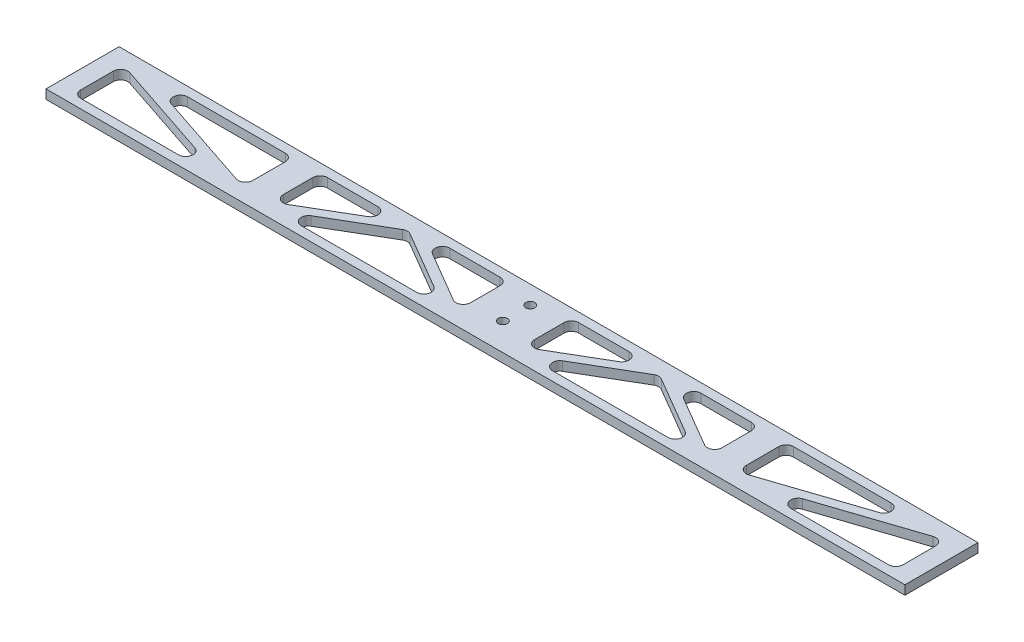
SolidWorks part; units mm, degrees
material "Plywood"
ref_plane "Front Plane" through (0, 0, 0) normal (0, 0, 1) x (1, 0, 0)
ref_plane "Top Plane" through (0, 0, 0) normal (0, 1, 0) x (1, 0, 0)
ref_plane "Right Plane" through (0, 0, 0) normal (1, 0, 0) x (0, 0, -1)
sketch "Sketch1" plane through (0, 0, 0) normal (0, 1, 0) x (1, 0, 0)
  line L1 (149.225, -12.7) -> (-149.225, -12.7)
  line L2 (149.225, -12.7) -> (149.225, 12.7)
  line L3 (149.225, 12.7) -> (-149.225, 12.7)
  line L4 (-149.225, -12.7) -> (-149.225, 12.7)
  point P0 (0, 12.7)
  point P6 (-149.225, 0)
  dimension "D1" = 25.4
  dimension "D2" = 298.45
extrude "Boss-Extrude1" add sketch "Sketch1" along normal blind 3.175
sketch "Sketch2" plane through (0, 3.175, 0) normal (0, 1, 0) x (1, 0, 0)
  line L0 (149.225, -12.7) -> (149.225, 12.7) construction
  line L2 (-149.225, 12.7) -> (-149.225, -12.7) construction
  line L4 (149.225, -12.7) -> (149.225, 12.7)
  line L6 (-149.225, 12.7) -> (-149.225, -12.7)
  line L8 (149.225, 9.525) -> (-149.225, 9.525)
  line L9 (-149.225, -9.525) -> (149.225, -9.525)
  line L10 (-142.875, 9.525) -> (-142.875, -9.525)
  line L11 (-80.9625, 9.525) -> (-80.9625, -9.525) construction
  line L12 (142.875, 9.525) -> (142.875, -9.525)
  line L13 (0, -9.525) -> (0, 9.525) construction
  line L14 (11.1125, 9.525) -> (11.1125, -9.525)
  line L15 (-11.1125, 9.525) -> (-11.1125, -9.525)
  line L16 (-85.725, 9.525) -> (-85.725, -9.525)
  line L17 (-76.2, 9.525) -> (-76.2, -9.525)
  line L18 (80.9625, 9.525) -> (80.9625, -9.525) construction
  line L19 (85.725, 9.525) -> (85.725, -9.525)
  line L20 (76.2, 9.525) -> (76.2, -9.525)
  line L21 (-76.2, -9.525) -> (-43.6562, 9.525)
  line L22 (-43.6562, 9.525) -> (-11.1125, -9.525)
  line L23 (-85.725, -9.525) -> (-142.875, 9.525)
  line L24 (11.1125, -9.525) -> (43.6562, 9.525)
  line L25 (43.6562, 9.525) -> (76.2, -9.525)
  line L26 (85.725, -9.525) -> (142.875, 9.525)
  line L27 (-85.223, -8.019) -> (-142.373, 11.031)
  line L28 (-75.398, -10.895) -> (-43.6562, 7.6855)
  line L29 (-43.6562, 7.6855) -> (-11.9145, -10.895)
  line L30 (11.9145, -10.895) -> (43.6562, 7.6855)
  line L31 (43.6562, 7.6855) -> (75.398, -10.895)
  line L32 (86.227, -11.031) -> (143.377, 8.019)
  line L33 (-86.227, -11.031) -> (-143.377, 8.019)
  line L34 (-77.002, -8.155) -> (-43.6562, 11.3645)
  line L35 (-43.6562, 11.3645) -> (-10.3105, -8.155)
  line L36 (10.3105, -8.155) -> (43.6562, 11.3645)
  line L37 (43.6562, 11.3645) -> (77.002, -8.155)
  line L38 (85.223, -8.019) -> (142.373, 11.031)
  dimension "D1" = 3.175
  dimension "D2" = 3.175
  dimension "D3" = 6.35
  dimension "D4" = 6.35
  dimension "D11" = 4.7625
  dimension "D12" = 4.7625
  dimension "D8" = 9.525
  dimension "D9" = 4.7625
  dimension "D7" = 63.5
  dimension "D10" = 63.5
  dimension "D5" = 22.225
  dimension "D6" = 11.1125
  dimension "D13" = 1.5875
  dimension "D14" = 1.5875
extrude "Cut-Extrude1" cut sketch "Sketch2" against normal through all contours L9 L33 L10 | L27 L16 L8 | L17 L34 L8 | L29 L28 L9 | L8 L35 L15 | L14 L36 L8 | L31 L30 L9 | L8 L37 L20 | L19 L38 L8 | L32 L9 L12
sketch "Sketch3" plane through (0, 3.175, 0) normal (0, 1, 0) x (1, 0, 0)
  circle A0 centre (0, 6.35) radius 1.5875
  circle A1 centre (0, -3.175) radius 1.5875
  dimension "D1" = 3.175
  dimension "D2" = 9.525
  dimension "D3" = 6.35
extrude "Cut-Extrude2" cut sketch "Sketch3" against normal through all
fillet "Fillet1" radius 2.54 30 edges at (-14.2549, 1.5875, 9.525) (-73.0576, 1.5875, 9.525) (-43.6562, 1.5875, -7.6855) (-11.1125, 1.5875, 7.6855) (-40.5138, 1.5875, -9.525) (-11.1125, 1.5875, -9.525) (-46.7987, 1.5875, -9.525) (-76.2, 1.5875, 7.6855) (-76.2, 1.5875, -9.525) (73.0576, 1.5875, 9.525) (14.2549, 1.5875, 9.525) (43.6562, 1.5875, -7.6855) (142.875, 1.5875, -7.8516) (142.875, 1.5875, 9.525) (90.7451, 1.5875, 9.525) (40.5138, 1.5875, -9.525) (11.1125, 1.5875, 7.6855) (11.1125, 1.5875, -9.525) (76.2, 1.5875, 7.6855) (46.7987, 1.5875, -9.525) (76.2, 1.5875, -9.525) (137.8549, 1.5875, -9.525) (85.725, 1.5875, 7.8516) (85.725, 1.5875, -9.525) (-137.8549, 1.5875, -9.525) (-85.725, 1.5875, 7.8516) (-85.725, 1.5875, -9.525) (-90.7451, 1.5875, 9.525) (-142.875, 1.5875, 9.525) (-142.875, 1.5875, -7.8516)
move or copy body "Body-Move/Copy1" [suppressed] bodies to move or copy 103 parameters "D1"=0, "D2"=0, "D3"=0
equation "\"D10@Sketch2\"=\"D7@Sketch2\""
equation "\"D6@Sketch2\"=\"D5@Sketch2\"/2"
